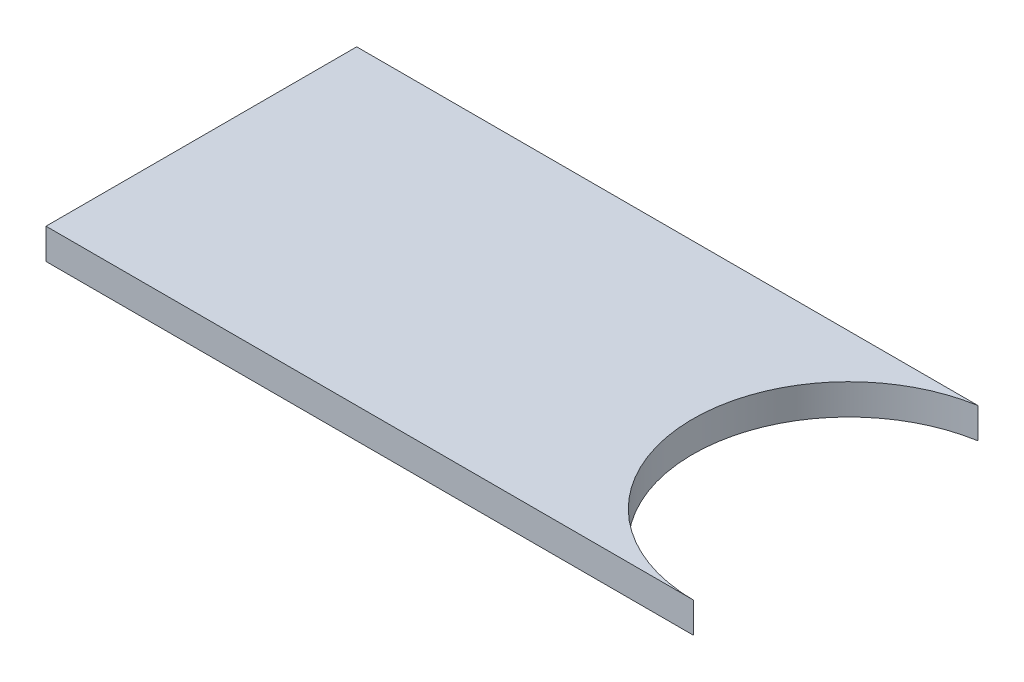
SolidWorks part; units mm, degrees
ref_plane "Front Plane" through (0, 0, 0) normal (0, 0, 1) x (1, 0, 0)
ref_plane "Top Plane" through (0, 0, 0) normal (0, 1, 0) x (1, 0, 0)
ref_plane "Right Plane" through (0, 0, 0) normal (1, 0, 0) x (0, 0, -1)
sketch "Sketch1" plane through (0, 0, 0) normal (0, 1, 0) x (1, 0, 0)
  line L0 (0, 0) -> (0, 60.96)
  line L1 (0, 60.96) -> (121.9087, 60.96)
  line L2 (0, 0) -> (127, 0)
  ellipse E0 centre (127.1241, 30.6997) end of major axis (96.2016, 30.7734) minor radius 30.6999 (121.9087, 60.96) -> (127, 0) ccw
extrude "Boss-Extrude1" add sketch "Sketch1" along normal blind 6 contours L1 E0 L2 L0
